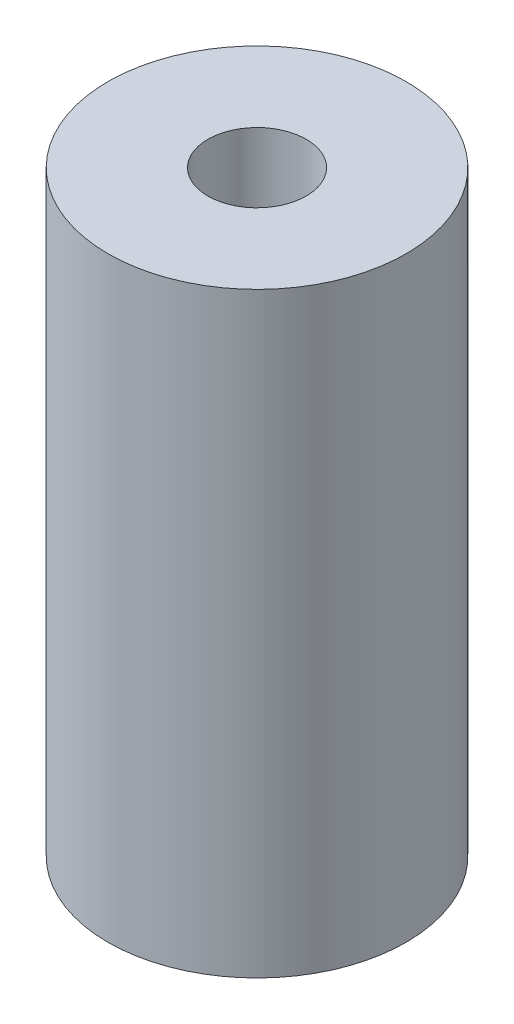
SolidWorks part; units mm, degrees
material "6061 Alloy"
ref_plane "Front Plane" through (0, 0, 0) normal (0, 0, 1) x (1, 0, 0)
ref_plane "Top Plane" through (0, 0, 0) normal (0, 1, 0) x (1, 0, 0)
ref_plane "Right Plane" through (0, 0, 0) normal (1, 0, 0) x (0, 0, -1)
sketch "Sketch1" plane through (0, 0, 0) normal (0, 1, 0) x (1, 0, 0)
  circle A0 centre (0, 0) radius 5
  dimension "D1" = 10
extrude "Boss-Extrude1" add sketch "Sketch1" along normal blind 20
hole_wizard "M4x0.7 Tapped Hole1" positions "Sketch2" profile "Sketch4" tap size "M4x0.7" standard "ANSI Metric" end condition through all
sketch "Sketch2" plane through (0, 20, 0) normal (0, 1, 0) x (1, 0, 0)
  point P0 (0, 0)
sketch "Sketch4" plane through (0, 20, 0) normal (1, 0, 0) x (0, 0, 1)
  line L0 (0, 0) -> (0, 20)
  line L1 (0, 20) -> (1.65, 20)
  line L2 (1.65, 20) -> (1.65, 0)
  line L5 (1.65, 0) -> (0, 0)
  line L11 (0, -6.35) -> (0, 107.95) construction
  dimension "Thru Tap Drill Dia." = 3.3
  dimension "Thru Tap Drill Depth" = 20
cosmetic thread "Hole Thread1" parameters "D2"=4
